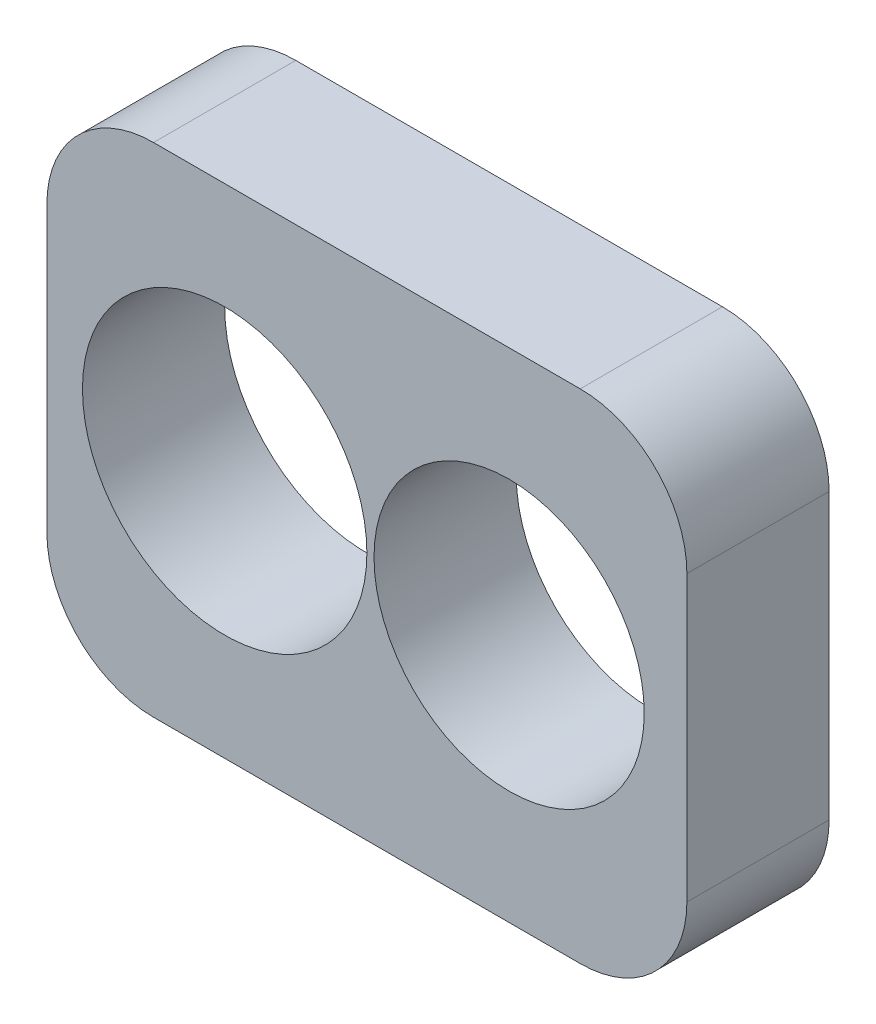
SolidWorks part; units mm, degrees
ref_plane "Front Plane" through (0, 0, 0) normal (0, 0, 1) x (1, 0, 0)
ref_plane "Top Plane" through (0, 0, 0) normal (0, 1, 0) x (1, 0, 0)
ref_plane "Right Plane" through (0, 0, 0) normal (1, 0, 0) x (0, 0, -1)
sketch "Sketch1" plane through (0, 0, 0) normal (0, 0, 1) x (1, 0, 0)
  line L1 (30, -35) -> (-30, -35)
  line L2 (45, -20) -> (45, 20)
  line L3 (30, 35) -> (-30, 35)
  line L4 (-45, -20) -> (-45, 20)
  line L5 (45, -35) -> (-45, 35) construction
  line L6 (45, 35) -> (-45, -35) construction
  arc A0 (-30, -35) -> (-45, -20) centre (-30, -20) cw
  arc A1 (30, -35) -> (45, -20) centre (30, -20) ccw
  arc A2 (45, 20) -> (30, 35) centre (30, 20) ccw
  arc A3 (-45, 20) -> (-30, 35) centre (-30, 20) cw
  point P0 (0, 0)
  dimension "D1" = 15
  dimension "D2" = 60
  dimension "D3" = 40
extrude "Boss-Extrude1" add sketch "Sketch1" along normal blind 20
sketch "Sketch3" plane through (0, 0, 20) normal (0, 0, 1) x (1, 0, 0)
  line L0 (-45, 20) -> (-45, -20) construction
  circle A0 centre (-20, 0) radius 20
  point P4 (-45, 0)
  dimension "D1" = 40
  dimension "D2" = 25
extrude "Cut-Extrude2" cut sketch "Sketch3" against normal through all and the other way through all
sketch "Sketch4" plane through (0, 0, 20) normal (0, 0, 1) x (1, 0, 0)
  circle A0 centre (20, 0) radius 19
  circle A1 centre (-20, 0) radius 20 construction
  dimension "D1" = 38
  dimension "D2" = 40
extrude "Cut-Extrude3" cut sketch "Sketch4" against normal through all
